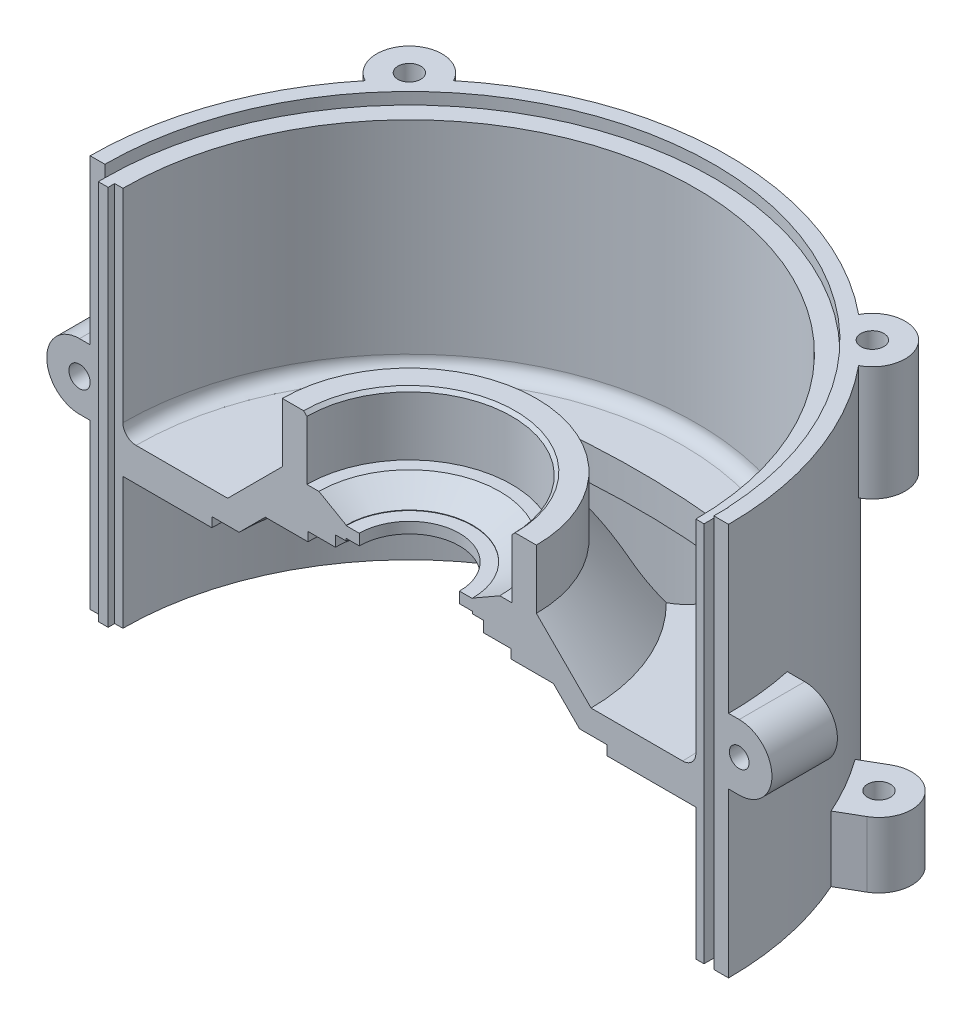
SolidWorks part; units mm, degrees
ref_plane "Plano frontal" through (0, 0, 0) normal (0, 0, 1) x (1, 0, 0)
ref_plane "Plano superior" through (0, 0, 0) normal (0, 1, 0) x (1, 0, 0)
ref_plane "Plano direito" through (0, 0, 0) normal (1, 0, 0) x (0, 0, -1)
sketch "Esboço3" plane through (0, 0, 0) normal (0, 0, 1) x (1, 0, 0)
  line L2 (97.5, 79.8) -> (97.5, 11.3045)
  line L4 (87.5, 0) -> (60.3424, 0)
  line L5 (31.3, 25.96) -> (27.6265, 25.96)
  line L6 (60.3424, 0) -> (60.3424, 2.95)
  line L7 (60.3424, 2.95) -> (52, 2.95)
  line L8 (52, 2.95) -> (44, 10.95)
  line L9 (44, 10.95) -> (31, 10.95)
  line L10 (31, 10.95) -> (31, 13.7)
  line L11 (31, 13.7) -> (22.6, 13.7)
  line L12 (22.6, 13.7) -> (22.6, 17)
  line L13 (22.6, 17) -> (19.3, 17)
  line L14 (19.3, 17) -> (19.3, 17.7)
  line L15 (19.3, 17.7) -> (15.3, 17.7)
  line L16 (15.3, 17.7) -> (15.3, 21.05)
  line L17 (15.3, 21.05) -> (19.3, 21.05)
  line L18 (97.5, 79.8) -> (93, 79.8)
  line L19 (93, 79.8) -> (93, 76.2)
  line L20 (93, 76.2) -> (87.5, 76.2)
  line L21 (87.5, 76.2) -> (87.5, 14.2)
  line L22 (83.5, 10.2) -> (55.5, 10.2)
  line L23 (55.5, 10.2) -> (38.8, 26.9)
  line L24 (38.8, 26.9) -> (38.8, 44.96)
  line L25 (38.8, 44.96) -> (32.3, 44.96)
  line L26 (32.3, 44.96) -> (31.3, 43.96)
  line L27 (31.3, 43.96) -> (31.3, 25.96)
  line L29 (19.3, 21.05) -> (19.3, 21.2)
  line L30 (55, 0) -> (-55, 0) construction
  line L31 (27.6265, 25.96) -> (19.3, 21.2)
  line L33 (97.5, 0) -> (97.5, 11.3045)
  line L34 (97.5, 0) -> (97.5, -40.2)
  line L35 (97.5, -40.2) -> (87.5, -40.2)
  line L36 (87.5, -40.2) -> (87.5, 0)
  arc A1 (87.5, 14.2) -> (83.5, 10.2) centre (83.5, 14.2) cw
  dimension "D32" = 79.8
  dimension "D2" = 7.5
  dimension "D3" = 135
  dimension "D4" = 19
  dimension "D5" = 120
  dimension "D6" = 0.15
  dimension "D7" = 135
  dimension "D8" = 16
  dimension "D9" = 34.84
  dimension "D10" = 28
  dimension "D11" = 66
  dimension "D12" = 3.6
  dimension "D13" = 93
  dimension "D14" = 10
  dimension "D15" = 17.7
  dimension "D16" = 1
  dimension "D17" = 31.3
  dimension "D18" = 10
  dimension "D19" = 52
  dimension "D20" = 44
  dimension "D21" = 135
  dimension "D22" = 31
  dimension "D23" = 22.6
  dimension "D24" = 19.3
  dimension "D25" = 15.3
  dimension "D26" = 2.75
  dimension "D27" = 3.3
  dimension "D28" = 0.7
  dimension "D29" = 3.35
  dimension "D31" = 97.5
ref_axis "Eixo1" through (0, -3.3221, 0) along (0, 1, 0)
revolve "Revolução2" add sketch "Esboço3" angle 180 about axis through (0, -3.3221, 0) along (0, 1, 0)
sketch "Esboço4" plane through (0, 79.8, 0) normal (0, 1, 0) x (1, 0, 0)
  line L0 (70.71, 70.71) -> (-70.71, 70.71) construction
  line L1 (-70.71, 70.71) -> (-70.71, -70.71) construction
  line L2 (-70.71, -70.71) -> (70.71, -70.71) construction
  line L3 (70.71, -70.71) -> (70.71, 70.71) construction
  line L4 (-55, 0) -> (55, 0) construction
  line L5 (0, -55) -> (0, 55) construction
  circle A0 centre (70.71, 70.71) radius 10
  circle A3 centre (-70.71, 70.71) radius 10
  point P0 (70.71, 0)
  point P8 (0, -70.71)
  dimension "D2" = 20
  dimension "D1" = 141.42
extrude "Ressalto-extrusão1" add sketch "Esboço4" against normal blind 35
sketch "Esboço5" plane through (0, -40.2, 0) normal (0, -1, 0) x (1, 0, 0)
  line L0 (0, 0) -> (70.71, -70.71) construction
  line L1 (0, 0) -> (0, -105) construction
  line L2 (10, -105) -> (10, -96.9858)
  line L3 (-10, -105) -> (-10, -96.9858)
  line L4 (10, -96.9858) -> (-10, -96.9858)
  arc A1 (10, -105) -> (-10, -105) centre (0, -105) cw
  arc A3 (-97.5, 0) -> (97.5, 0) centre (0, 0) ccw construction
  dimension "D2" = 10
  dimension "D1" = 105
extrude "Ressalto-extrusão2" add sketch "Esboço5" against normal blind 20
sketch "Esboço8" plane through (0, -40.2, 0) normal (0, -1, 0) x (1, 0, 0)
  circle A0 centre (0, -105) radius 3.5
  dimension "D1" = 7
extrude "Corte-extrusão2" cut sketch "Esboço8" against normal blind 20
pattern_circular "PadrãoCircular1" count 6 over 360 about axis through (0, 0, 0) along (0, 1, 0) of "Ressalto-extrusão2", "Corte-extrusão2"
sketch "Esboço6" plane through (0, 79.8, 0) normal (0, 1, 0) x (1, 0, 0)
  circle A2 centre (70.71, 70.71) radius 3.5
  circle A3 centre (-70.71, 70.71) radius 3.5
  dimension "D1" = 7
extrude "Corte-extrusão1" cut sketch "Esboço6" against normal blind 15
sketch "Esboço9" plane through (0, 13.7, 0) normal (0, -1, 0) x (1, 0, 0)
  line L0 (0, 0) -> (18.7383, -18.7383) construction
  line L1 (-18.7383, -18.7383) -> (0, 0) construction
  line L2 (-18.7383, -18.7383) -> (18.7383, -18.7383) construction
  circle A2 centre (18.7383, -18.7383) radius 1.25
  circle A3 centre (-18.7383, -18.7383) radius 1.25
  point P13 (4.0879, -3.0957)
  dimension "D2" = 26.5
  dimension "D1" = 26.5
extrude "Corte-extrusão3" cut sketch "Esboço9" against normal blind 6
sketch "Esboço10" plane through (0, 0, 0) normal (0, 0, 1) x (1, 0, 0)
  line L0 (93, -40.2) -> (93, 79.8)
  line L2 (97.5, 79.8) -> (93, 79.8) construction
  line L3 (93, 79.8) -> (90, 79.8)
  line L4 (93, 79.8) -> (70.4477, 79.8) construction
  line L5 (90, 79.8) -> (90, -40.2)
  line L6 (90, -40.2) -> (93, -40.2)
  line L7 (87.5, -40.2) -> (97.5, -40.2) construction
  dimension "D1" = 3
extrude "Corte-extrusão4" cut sketch "Esboço10" against normal blind 4.5
sketch "Esboço11" plane through (0, 0, 0) normal (0, 0, 1) x (1, 0, 0)
  line L0 (-90, -40.2) -> (-90, 76.2)
  line L2 (-87.5, -40.2) -> (-97.5, -40.2) construction
  line L3 (-90, 76.2) -> (-93, 76.2)
  line L4 (-93, 76.2) -> (-93, -40.2)
  line L5 (-93, -40.2) -> (-90, -40.2)
  line L6 (-93, 79.8) -> (-93, 76.2) construction
  line L7 (-93, 76.2) -> (-87.5, 76.2) construction
  dimension "D1" = 3
extrude "Ressalto-extrusão5" add sketch "Esboço11" along normal blind 2
sketch "Esboço12" plane through (0, 0, 0) normal (0, 0, 1) x (1, 0, 0)
  line L0 (-124.1305, 19.8) -> (136.9824, 19.8) construction
  line L2 (-97.5, -40.2) -> (-97.5, 79.8) construction
  line L3 (-100.75, 9.8) -> (-100.75, 29.8) construction
  line L4 (-100.75, 29.8) -> (-87.5, 29.8)
  line L5 (-87.5, 76.2) -> (-87.5, 14.2) construction
  line L6 (-87.5, 29.8) -> (-87.5, 9.8)
  line L7 (-87.5, 9.8) -> (-100.75, 9.8)
  arc A1 (-100.75, 9.8) -> (-100.75, 29.8) centre (-100.75, 19.8) cw
  circle A2 centre (-100.75, 19.8) radius 3.25
  point P8 (-97.5, 19.8)
  dimension "D2" = 6.5
  dimension "D1" = 20
extrude "Ressalto-extrusão6" add sketch "Esboço12" against normal blind 20
sketch "Esboço13" plane through (0, 0, 0) normal (0, 0, 1) x (1, 0, 0)
  line L0 (100.75, 29.8) -> (100.75, 9.8) construction
  line L3 (-100.75, 19.8) -> (140.3594, 19.8) construction
  line L4 (100.75, 29.8) -> (93, 29.8)
  line L5 (93, 29.8) -> (93, 9.8)
  line L6 (93, 9.8) -> (100.75, 9.8)
  line L7 (93, -40.2) -> (93, 79.8) construction
  line L8 (97.5, -40.2) -> (97.5, 79.8) construction
  arc A0 (100.75, 9.8) -> (100.75, 29.8) centre (100.75, 19.8) ccw
  circle A1 centre (100.75, 19.8) radius 3
  dimension "D3" = 6
  dimension "D1" = 20
  dimension "D2" = 3.25
extrude "Ressalto-extrusão7" add sketch "Esboço13" against normal blind 20
sketch "Esboço14" plane through (0, 0, 0) normal (0, -1, 0) x (-1, 0, 0)
  line L0 (0, -185) -> (0, 115) construction
  arc A0 (32.1753, 52.6546) -> (-32.1753, 52.6546) centre (0, -166.8724) ccw construction
  arc A1 (34.3505, 67.4961) -> (-34.3505, 67.4961) centre (0, -166.8724) ccw
  arc A2 (30, 37.8132) -> (-30, 37.8132) centre (0, -166.8724) ccw
  arc A3 (30, 37.8132) -> (34.3505, 67.4961) centre (32.1753, 52.6546) ccw
  arc A4 (-34.3505, 67.4961) -> (-30, 37.8132) centre (-32.1753, 52.6546) ccw
  arc A5 (10, 105) -> (-10, 105) centre (0, 105) ccw construction
  point P3 (0, 55)
  point P8 (0, 0)
  point P9 (0, 0)
  point P10 (3.9113, 14.7916)
  point P11 (-6.5142, 21.8237)
  point P12 (0, 0)
  point P13 (0, 21.6748)
  point P14 (0, 0)
  point P16 (0.0008, 79.3116)
  point P17 (-0.0015, -17.1269)
  point P25 (0, -40.3889)
  point P26 (-0.0027, -47.5789)
  point P27 (1.2753, -63.0988)
  point P28 (7.4015, -126.6629)
  point P30 (-1.832, -126.6626)
  point P31 (0, 0)
  point P32 (0, -146.1017)
  point P34 (0, 55.5)
  point P35 (0, 0)
  point P36 (0, 67.1553)
  point P37 (0, 0)
  point P38 (0, 0)
  point P39 (-1.832, -264.9232)
  point P40 (-1.832, -202.7371)
  point P41 (-1.832, -178.9806)
  point P43 (-5.6293, -102.2034)
  point P44 (0, -159.3724)
  dimension "D1" = 30
  dimension "D2" = 300
  dimension "D3" = 55
  dimension "D4" = 60
extrude "Corte-extrusão5" cut sketch "Esboço14" against normal through all
sketch "Esboço16" plane through (0, 76.2, 0) normal (0, 1, 0) x (1, 0, 0)
  circle A0 centre (0, 0) radius 93
extrude "Corte-extrusão6" cut sketch "Esboço16" along normal blind 10
